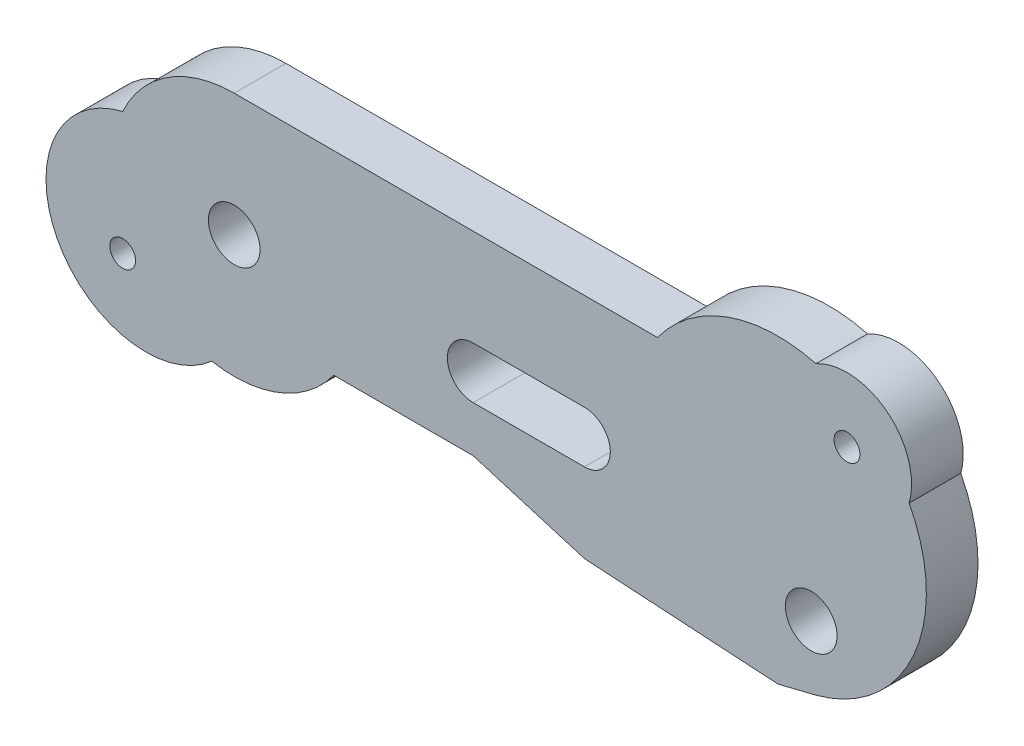
SolidWorks part; units mm, degrees
ref_plane "Front Plane" through (0, 0, 0) normal (0, 0, 1) x (1, 0, 0)
ref_plane "Top Plane" through (0, 0, 0) normal (0, 1, 0) x (1, 0, 0)
ref_plane "Right Plane" through (0, 0, 0) normal (1, 0, 0) x (0, 0, -1)
sketch "Sketch1" plane through (0, 0, 0) normal (0, 0, 1) x (1, 0, 0)
  line L0 (0, 9.5) -> (32.7687, 9.5)
  line L1 (7.7015, -5.5622) -> (18.5015, -5.5622)
  line L2 (18.5015, -5.5622) -> (27.1204, -8.1533)
  line L3 (27.1204, -8.1533) -> (42.0921, -9.0736)
  line L4 (18.5015, 2) -> (27.1204, 2)
  line L5 (18.5015, -2) -> (27.1204, -2)
  line L6 (42.0921, -9.0736) -> (44.9993, -8.3587)
  arc A0 (0, 9.5) -> (-8.6377, 3.9548) centre (0, 0) ccw
  arc A1 (-8.6377, 3.9548) -> (-1.7344, -9.3403) centre (-6.8535, -3.5586) ccw
  arc A2 (44.6766, -8.438) -> (52.2593, 8.1416) centre (42.0921, 2.7678) ccw
  arc A3 (52.2593, 8.1416) -> (45.0415, 13.8831) centre (47.4474, 9.5) ccw
  arc A4 (18.5015, 2) -> (18.5015, -2) centre (18.5015, 0) ccw
  arc A5 (27.1204, -2) -> (27.1204, 2) centre (27.1204, 0) ccw
  arc A6 (45.0415, 13.8831) -> (32.7687, 9.5) centre (42.0921, 2.7678) ccw
  circle A7 centre (47.4474, 9.5) radius 1
  circle A8 centre (44.6766, -3.5586) radius 2
  arc A9 (-1.7344, -9.3403) -> (7.7015, -5.5622) centre (0, 0) ccw
  circle A10 centre (0, 0) radius 2
  circle A11 centre (-8.6377, -5.5622) radius 1
extrude "Boss-Extrude1" add sketch "Sketch1" along normal blind 4 contours A1 A9 L1 L2 L3 L6 A2 A3 A6 L0 A0 A11 A10 A5 L5 A4 L4 A7 A8
